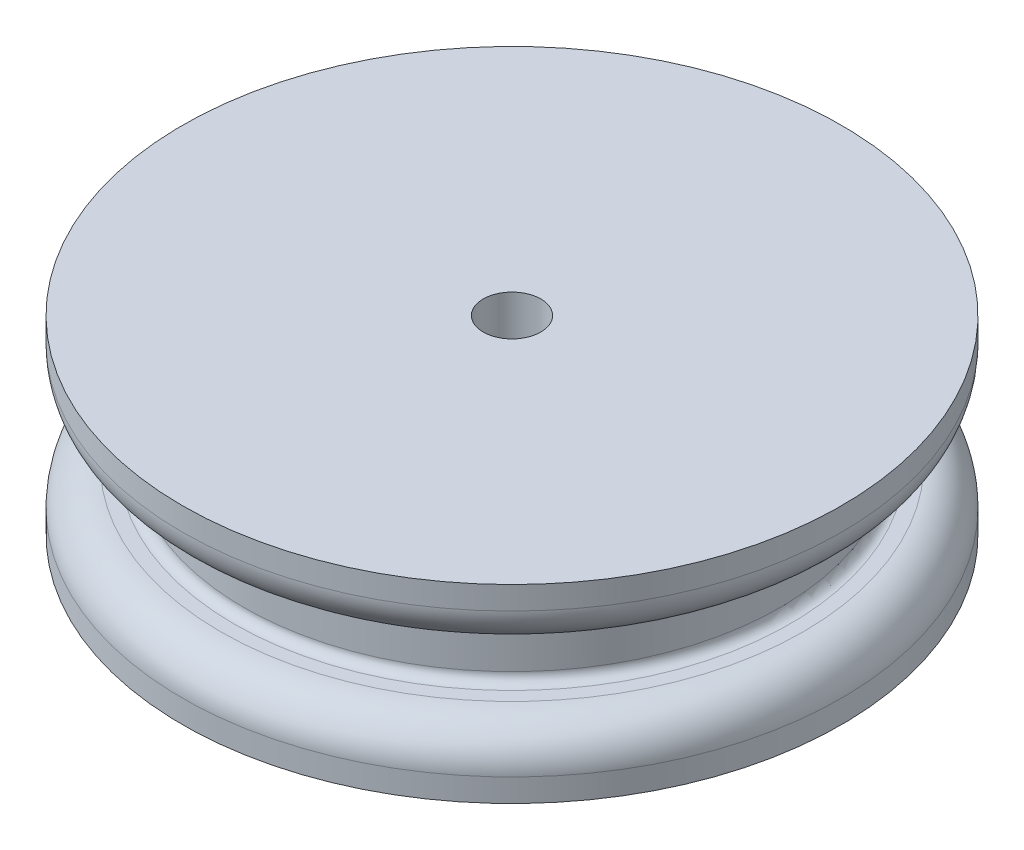
SolidWorks part; units mm, degrees
ref_plane "Front Plane" through (0, 0, 0) normal (0, 0, 1) x (1, 0, 0)
ref_plane "Top Plane" through (0, 0, 0) normal (0, 1, 0) x (1, 0, 0)
ref_plane "Right Plane" through (0, 0, 0) normal (1, 0, 0) x (0, 0, -1)
sketch "Croquis1" plane through (0, 0, 0) normal (0, 1, 0) x (1, 0, 0)
  circle A0 centre (0, 0) radius 14
  dimension "D1" = 28
extrude "Saliente-Extruir1" add sketch "Croquis1" along normal blind 3.5
sketch "Croquis2" plane through (0, 3.5, 0) normal (0, 1, 0) x (1, 0, 0)
  circle A0 centre (0, 0) radius 17.2
  circle A1 centre (0, 0) radius 14 construction
  dimension "D1" = 3.2
extrude "Saliente-Extruir2" add sketch "Croquis2" along normal blind 3.2
sketch "Croquis3" plane through (0, 0, 0) normal (0, -1, 0) x (1, 0, 0)
  circle A0 centre (0, 0) radius 17.2 construction
  circle A1 centre (0, 0) radius 17.2
extrude "Saliente-Extruir3" add sketch "Croquis3" along normal blind 3.2
sketch "Croquis4" plane through (0, -3.2, 0) normal (0, -1, 0) x (1, 0, 0)
  circle A0 centre (0, 0) radius 1.5
  dimension "D1" = 3
extrude "Cortar-Extruir1" cut sketch "Croquis4" against normal through all
fillet "Redondeo1" radius 2 2 edges at (0, 3.5, 17.2) (0, 0, -17.2)
fillet "Redondeo2" radius 0.5 2 edges at (0, 3.5, 14) (0, 0, 14)
